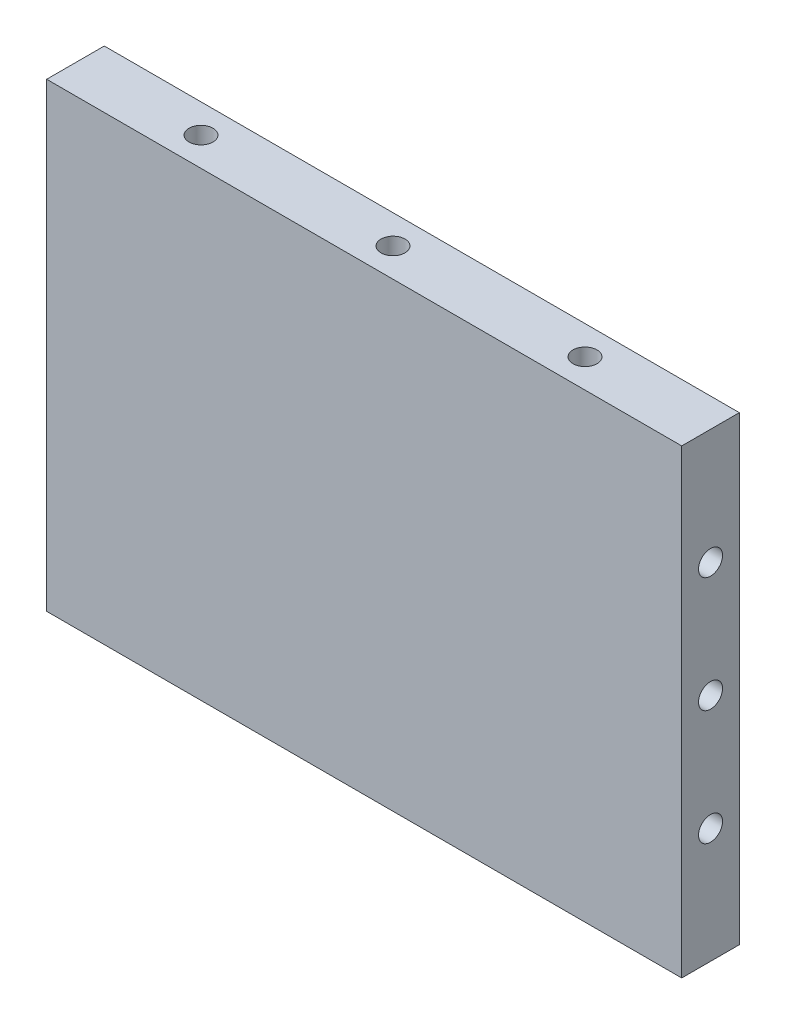
SolidWorks part; units mm, degrees
material "6063-T5"
ref_plane "前视基准面" through (0, 0, 0) normal (0, 0, 1) x (1, 0, 0)
ref_plane "上视基准面" through (0, 0, 0) normal (0, 1, 0) x (1, 0, 0)
ref_plane "右视基准面" through (0, 0, 0) normal (1, 0, 0) x (0, 0, -1)
other "Configuration Table"
sketch "草图1" plane through (0, 0, 0) normal (0, 0, 1) x (1, 0, 0)
  line L1 (-33.075, -24) -> (33.075, -24)
  line L2 (-33.075, -24) -> (-33.075, 24)
  line L3 (-33.075, 24) -> (33.075, 24)
  line L4 (33.075, -24) -> (33.075, 24)
  line L5 (-33.075, -24) -> (33.075, 24) construction
  line L6 (-33.075, 24) -> (33.075, -24) construction
  point P0 (0, 0)
  dimension "D1" = 66.15
  dimension "D2" = 48
extrude "凸台-拉伸1" add sketch "草图1" along normal blind 6
sketch "草图2" plane through (0, 24, 0) normal (0, 1, 0) x (1, 0, 0)
  line L0 (0, 0) -> (0, 50000) construction
  line L1 (26.125, -3) -> (50026.125, -3) construction
  line L2 (33.075, -6) -> (33.075, 0) construction
  circle A0 centre (0, -3) radius 2.525
  circle A1 centre (-20, -3) radius 2.525
  circle A2 centre (20, -3) radius 2.525
  point P7 (33.075, -3)
  dimension "D1" = 5.05
  dimension "D2" = 20
sketch "草图9" plane through (0, 0, 6) normal (0, 0, 1) x (1, 0, 0)
  line L0 (33.075, -24) -> (33.075, 24) construction
  line L1 (-33.075, 24) -> (33.075, 24)
  line L2 (-33.075, 24) -> (-33.075, 30)
  line L3 (-33.075, 30) -> (33.075, 30)
  line L4 (33.075, 24) -> (33.075, 30)
  dimension "D1" = 6
sketch "草图5" plane through (-33.075, 0, 0) normal (-1, 0, 0) x (0, 0, 1)
  line L0 (3, 17.5) -> (3, 50017.5) construction
  line L1 (5.525, 24) -> (0.475, 24) construction
  line L2 (0, 0) -> (50000, 0) construction
  circle A0 centre (3, 12) radius 1.1739 construction
  circle A1 centre (3, -12) radius 1.1739 construction
  point P4 (3, 24)
  dimension "D1" = 2.3477
  dimension "D2" = 12
sketch "草图6" plane through (-33.075, 0, 0) normal (-1, 0, 0) x (0, 0, 1)
  line L0 (3, -199982.5) -> (3, 250017.5) construction
  line L1 (-200000, 0) -> (250000, 0) construction
  point P0 (3, 12)
  point P3 (3, -12)
  point P6 (3, 0)
hole_wizard "M3 螺纹孔2" positions "草图6" profile "草图7" tap size "M3" standard "GB" end condition through all
sketch "草图7" plane through (-33.075, 12, 3) normal (0, 1, 0) x (0, 0, 1)
  line L0 (0, 0) -> (0, 66.15)
  line L1 (0, 66.15) -> (1.25, 66.15)
  line L2 (1.25, 66.15) -> (1.25, 0)
  line L5 (1.25, 0) -> (0, 0)
  line L11 (0, -6.35) -> (0, 107.95) construction
  dimension "通孔螺纹孔钻头直径" = 2.5
  dimension "通孔螺纹孔钻头深度" = 66.15
cosmetic thread "孔螺蚊线4" parameters "D2"=3
cosmetic thread "孔螺蚊线5" parameters "D2"=3
cosmetic thread "孔螺蚊线6" parameters "D2"=3
sketch "草图10" plane through (0, 24, 0) normal (0, 1, 0) x (1, 0, 0)
  line L0 (-33.075, -3) -> (49966.925, -3) construction
  line L1 (-33.075, -6) -> (-33.075, 0) construction
  line L2 (0, 0) -> (0, -3) construction
  line L3 (0, -3) -> (0, 49997) construction
  circle A0 centre (0, -3) radius 1.525
  circle A1 centre (20, -3) radius 1.525
  circle A2 centre (-20, -3) radius 1.525
  point P4 (-33.075, -3)
  point P5 (0, -3)
  point P8 (20, -3)
  point P11 (-20, -3)
  point P22 (0, -3)
  dimension "D1" = 3.05
  dimension "D2" = 20
hole_wizard "M3 螺纹孔3" positions "草图10" profile "草图11" tap size "M3" standard "GB" end condition through all
sketch "草图11" plane through (0, 24, 3) normal (1, 0, 0) x (0, 0, 1)
  line L0 (0, 0) -> (0, 48)
  line L1 (0, 48) -> (1.25, 48)
  line L2 (1.25, 48) -> (1.25, 0)
  line L5 (1.25, 0) -> (0, 0)
  line L11 (0, -6.35) -> (0, 107.95) construction
  dimension "通孔螺纹孔钻头直径" = 2.5
  dimension "通孔螺纹孔钻头深度" = 48
cosmetic thread "孔螺蚊线7" parameters "D2"=3
cosmetic thread "孔螺蚊线8" parameters "D2"=3
cosmetic thread "孔螺蚊线10" parameters "D2"=3
